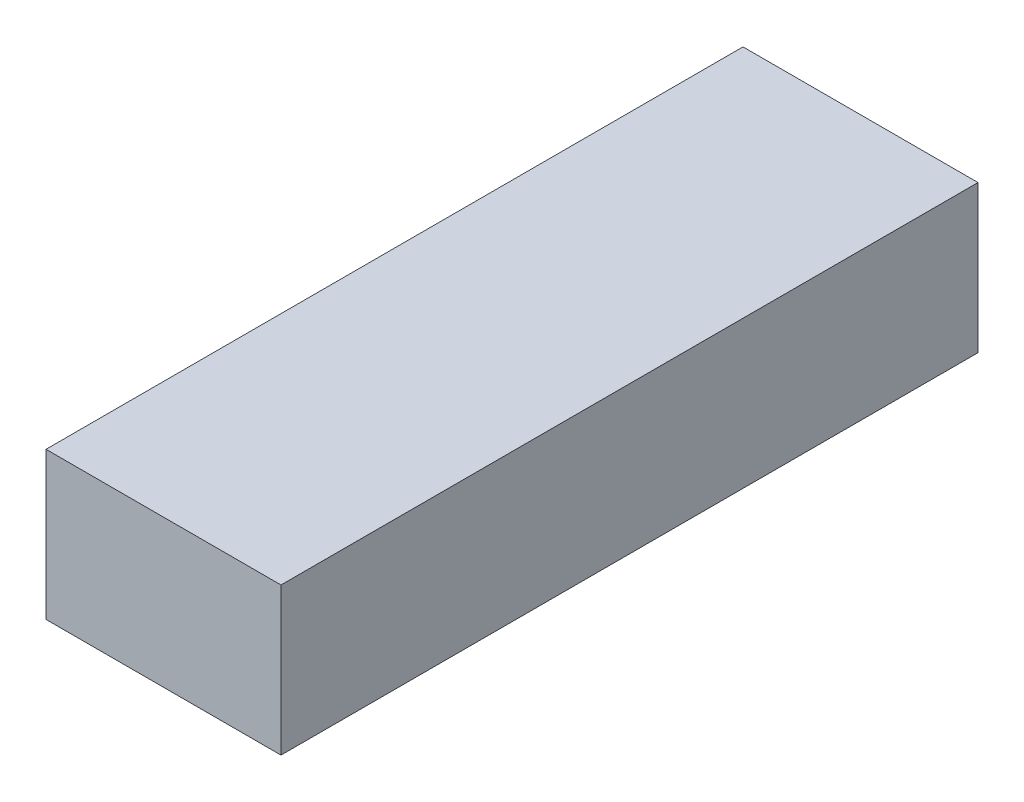
SolidWorks part; units mm, degrees
ref_plane "Front Plane" through (0, 0, 0) normal (0, 0, 1) x (1, 0, 0)
ref_plane "Top Plane" through (0, 0, 0) normal (0, 1, 0) x (1, 0, 0)
ref_plane "Right Plane" through (0, 0, 0) normal (1, 0, 0) x (0, 0, -1)
sketch "Sketch1" plane through (0, 0, 0) normal (0, 1, 0) x (1, 0, 0)
  line L0 (0, 17.3235) -> (0, -20.7882) construction
  line L1 (-3.9, 3.9) -> (3.9, 3.9)
  line L2 (-3.9, 3.9) -> (-3.9, -3.9)
  line L3 (-3.9, -3.9) -> (3.9, -3.9)
  line L4 (3.9, 3.9) -> (3.9, -3.9)
  line L5 (-3.9, 3.9) -> (3.9, -3.9) construction
  line L6 (-3.9, -3.9) -> (3.9, 3.9) construction
  line L7 (3.9, -3.9) -> (5.9, -3.9) construction
  line L8 (-5.9, 26.7) -> (5.9, 26.7)
  line L9 (-5.9, 26.7) -> (-5.9, -8.3)
  line L10 (-5.9, -8.3) -> (5.9, -8.3)
  line L11 (5.9, 26.7) -> (5.9, -8.3)
  line L12 (-5.9, 26.7) -> (5.9, -8.3) construction
  line L13 (-5.9, -8.3) -> (5.9, 26.7) construction
  point P0 (0, 0)
  point P7 (0, 9.2)
  dimension "D1" = 7.8
  dimension "D2" = 2
  dimension "D3" = 4.4
  dimension "D4" = 35
extrude "Boss-Extrude1" add sketch "Sketch1" along normal blind 2.8
sketch "Sketch2" plane through (0, 2.8, 0) normal (0, 1, 0) x (1, 0, 0)
  line L0 (-3.9, 3.9) -> (-3.9, -3.9) construction
  line L1 (-3.4, -3.4) -> (3.4, -3.4)
  line L2 (-3.4, -3.4) -> (-3.4, 3.4)
  line L3 (-3.4, 3.4) -> (3.4, 3.4)
  line L4 (5.9, -8.3) -> (5.9, 26.7)
  line L5 (5.9, 26.7) -> (-5.9, 26.7)
  line L6 (-5.9, 26.7) -> (-5.9, -8.3)
  line L7 (-5.9, -8.3) -> (5.9, -8.3)
  line L8 (5.9, -8.3) -> (5.9, 26.7)
  line L9 (5.9, 26.7) -> (-5.9, 26.7)
  line L10 (-5.9, 26.7) -> (-5.9, -8.3)
  line L11 (-5.9, -8.3) -> (5.9, -8.3)
  line L12 (3.4, -3.4) -> (3.4, 3.4)
  line L13 (-3.4, -3.4) -> (3.4, 3.4) construction
  line L14 (-3.4, 3.4) -> (3.4, -3.4) construction
  line L15 (-3.4, 3.4) -> (-3.9, 3.4) construction
  line L16 (-3.4, 3.4) -> (-3.4, 3.9) construction
  line L17 (3.9, 3.9) -> (-3.9, 3.9) construction
  line L18 (0, 26.7) -> (0, -8.3) construction
  line L20 (3.4, 24.7) -> (-3.4, 24.7)
  line L21 (3.4, 24.7) -> (3.4, 3.4)
  line L22 (3.4, 3.4) -> (-3.4, 3.4)
  line L23 (-3.4, 24.7) -> (-3.4, 3.4)
  line L24 (3.4, 24.7) -> (-3.4, 3.4) construction
  line L25 (3.4, 3.4) -> (-3.4, 24.7) construction
  point P2 (0, 0)
  point P18 (0, 14.05)
  line M12 (5.9, -8.3) -> (5.9, 26.7)
  line M13 (5.9, 26.7) -> (-5.9, 26.7)
  line M14 (-5.9, 26.7) -> (-5.9, -8.3)
  line M15 (-5.9, -8.3) -> (5.9, -8.3)
  line M16 (-3.9, 3.9) -> (3.9, 3.9)
  line M17 (3.9, 3.9) -> (3.9, -3.9)
  line M18 (3.9, -3.9) -> (-3.9, -3.9)
  line M19 (-3.9, -3.9) -> (-3.9, 3.9)
  dimension "D2" = 0.5
  dimension "D3" = 2
  dimension "D1" = 0
extrude "Boss-Extrude2" add sketch "Sketch2" along normal blind 3 contours L23 L20 L21 M15 M12 M13 M14 M16 M17 M18 M19 | L23 L21 L12 L1 L2 M16 M19 M18 M17
sketch "Sketch3" plane through (0, 5.8, 0) normal (0, 1, 0) x (1, 0, 0)
  line L4 (-5.9, -8.3) -> (5.9, -8.3)
  line L5 (5.9, -8.3) -> (5.9, 26.7)
  line L6 (5.9, 26.7) -> (-5.9, 26.7)
  line L7 (-5.9, 26.7) -> (-5.9, -8.3)
  line L8 (-5.9, -8.3) -> (5.9, -8.3)
  line L9 (5.9, -8.3) -> (5.9, 26.7)
  line L10 (5.9, 26.7) -> (-5.9, 26.7)
  line L11 (-5.9, 26.7) -> (-5.9, -8.3)
  dimension "D1" = 0
extrude "Boss-Extrude3" add sketch "Sketch3" along normal blind 1.6
ref_plane "Plane1" through (0, -4.566, -0.8051) normal (0, -0.9848, -0.1736) x (-1, 0, 0)
sketch "Sketch4" plane through (0, -4.566, -0.8051) normal (0, -0.9848, -0.1736) x (-1, 0, 0)
  line L0 (0, 26.2944) -> (0, -8.1739) construction
  line L1 (-5.9, 26.2944) -> (5.9, 26.2944) construction
  line L2 (5.9, -8.1739) -> (-5.9, -8.1739) construction
  line L3 (-5.9, 24.2944) -> (5.9, 24.2944) construction
  line L4 (-5.9, -8.1739) -> (-5.9, 26.2944) construction
  line L5 (5.9, 26.2944) -> (5.9, -8.1739) construction
  circle A0 centre (0, 20.1694) radius 4.125
  dimension "D1" = 8.25
  dimension "D2" = 2
extrude "Cut-Extrude1" cut sketch "Sketch4" against normal up to surface (6.2421 mm away)
equation "\"LedSize\"= 7.6"
equation "\"D1@Sketch1\"=\"LedSize\"+0.2"
